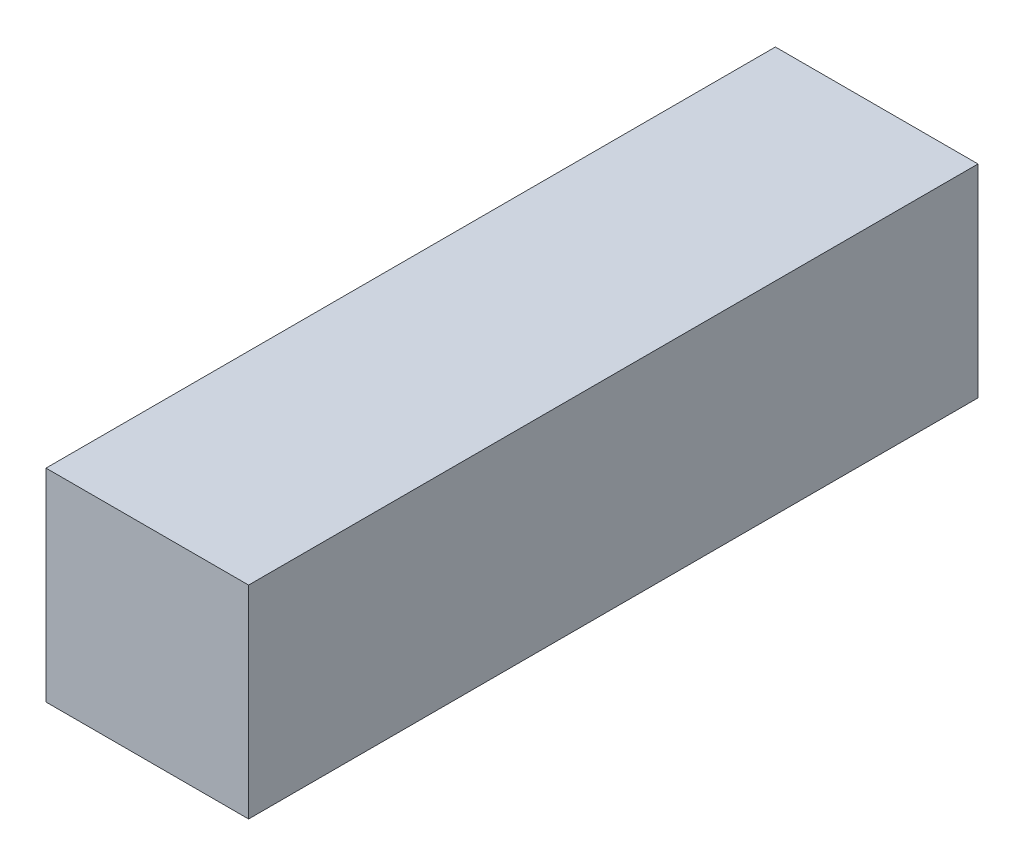
SolidWorks part; units mm, degrees
ref_plane "Plano frontal" through (0, 0, 0) normal (0, 0, 1) x (1, 0, 0)
ref_plane "Plano superior" through (0, 0, 0) normal (0, 1, 0) x (1, 0, 0)
ref_plane "Plano direito" through (0, 0, 0) normal (1, 0, 0) x (0, 0, -1)
sketch "Esboço2" plane through (0, 0, 0) normal (0, 0, 1) x (1, 0, 0)
  line L1 (-167.8931, 18.6709) -> (-117.8931, 18.6709)
  line L2 (-167.8931, 18.6709) -> (-167.8931, -31.3291)
  line L3 (-167.8931, -31.3291) -> (-117.8931, -31.3291)
  line L4 (-117.8931, 18.6709) -> (-117.8931, -31.3291)
  dimension "D1" = 50
  dimension "D2" = 50
extrude "Ressalto-extrusão1" add sketch "Esboço2" along normal blind 180
